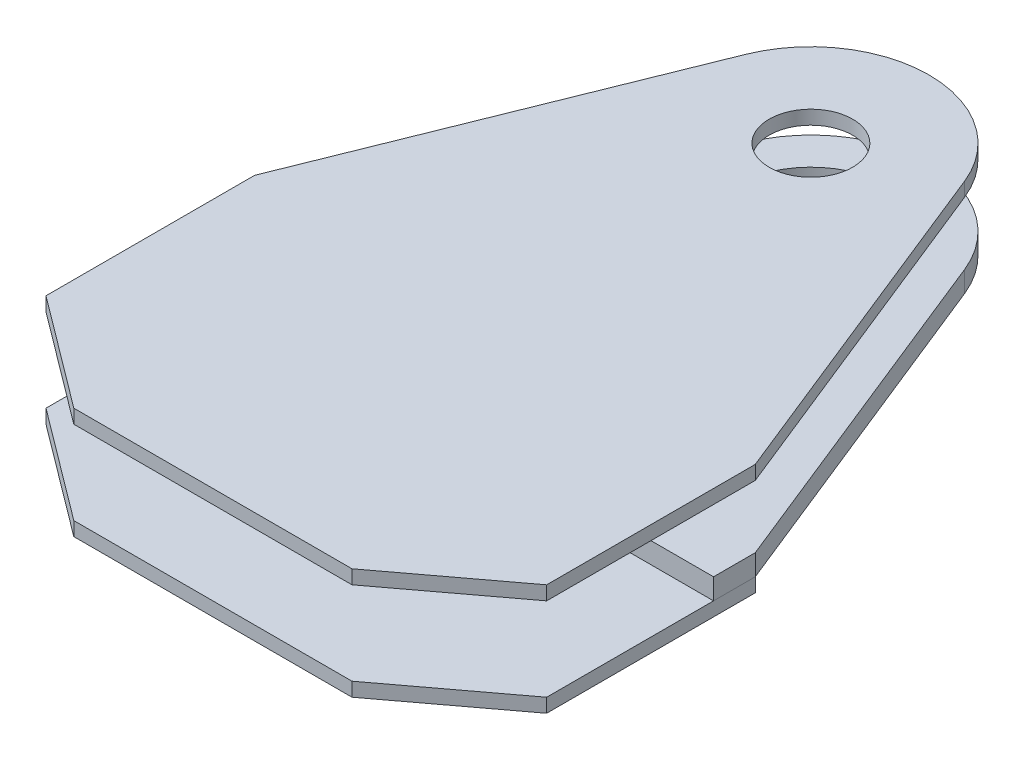
SolidWorks part; units mm, degrees
material "Alum Plate"
ref_plane "Front Plane" through (0, 0, 0) normal (0, 0, 1) x (1, 0, 0)
ref_plane "Top Plane" through (0, 0, 0) normal (0, 1, 0) x (1, 0, 0)
ref_plane "Right Plane" through (0, 0, 0) normal (1, 0, 0) x (0, 0, -1)
other "Center of Mass"
other "Bounding Box"
ref_plane "Default Plane" through (-8.9266, -12.7485, 0) normal (-0.1736, 0.9848, 0) x (0.9848, 0.1736, 0)
sketch "Sketch1" plane through (0, 0, 0) normal (0, 1, 0) x (1, 0, 0)
  line L0 (0, 0) -> (0, -177.8) construction
  line L1 (0, -177.8) -> (38.1, -177.8) construction
  line L2 (38.1, -177.8) -> (76.2, -177.8) construction
  line L3 (76.2, -191.8) -> (38.1, -191.8)
  line L4 (76.2, -191.8) -> (76.2, -163.8)
  line L5 (76.2, -163.8) -> (38.1, -163.8)
  line L6 (38.1, -191.8) -> (38.1, -163.8)
  line L7 (76.2, -191.8) -> (38.1, -163.8) construction
  line L8 (76.2, -163.8) -> (38.1, -191.8) construction
  line L9 (114.3, -195.8) -> (76.2, -195.8)
  line L10 (114.3, -195.8) -> (114.3, -159.8)
  line L11 (114.3, -159.8) -> (76.2, -159.8)
  line L12 (76.2, -195.8) -> (76.2, -159.8)
  line L13 (114.3, -195.8) -> (76.2, -159.8) construction
  line L14 (114.3, -159.8) -> (76.2, -195.8) construction
  line L15 (76.2, -177.8) -> (114.3, -177.8) construction
  line L16 (114.3, -177.8) -> (136.525, -177.8) construction
  line L17 (0, -177.8) -> (0, -196.85) construction
  line L18 (127, -215.9) -> (146.05, -215.9)
  line L19 (127, -215.9) -> (127, -139.7)
  line L20 (127, -139.7) -> (146.05, -139.7)
  line L21 (146.05, -215.9) -> (146.05, -139.7)
  line L22 (127, -215.9) -> (146.05, -139.7) construction
  line L23 (127, -139.7) -> (146.05, -215.9) construction
  circle A0 centre (0, 0) radius 165.1
  circle A1 centre (0, 0) radius 15
  circle A2 centre (0, 0) radius 36
  circle A3 centre (0, -196.85) radius 21
  point P5 (0, 36)
  point P6 (0, 165.1)
  point P7 (57.15, -177.8)
  point P16 (95.25, -177.8)
  point P26 (0, 15)
  point P29 (161.4153, -209.55)
  point P30 (0, -199.2951)
  dimension "D1" = 330.2
  dimension "D2" = 30
  dimension "D3" = 72
  dimension "D11" = 114.3
  dimension "D14" = 42
  dimension "D4" = 76.2
  dimension "D5" = 28
  dimension "D6" = 36
  dimension "D7" = 38.1
  dimension "D8" = 38.1
  dimension "D9" = 19.05
  dimension "D10" = 177.8
  dimension "D12" = 12.7
  dimension "D13" = 196.85
sketch "Sketch2" plane through (0, 0, 0) normal (1, 0, 0) x (0, 0, -1)
  line L0 (-250.4083, -38.1) -> (-147.3027, -38.1) construction
  line L1 (-165.1, -25.4) -> (165.1, -25.4)
  line L2 (-165.1, -25.4) -> (-165.1, -34.925)
  line L3 (-165.1, -34.925) -> (165.1, -34.925)
  line L4 (165.1, -25.4) -> (165.1, -34.925)
  line L5 (-165.1, -25.4) -> (165.1, -34.925) construction
  line L6 (-165.1, -34.925) -> (165.1, -25.4) construction
  line L7 (0, 0) -> (0, 32.1528) construction
  line L8 (-36, -19.05) -> (36, -19.05)
  line L9 (-36, -19.05) -> (-36, -0.05)
  line L10 (-36, -0.05) -> (36, -0.05)
  line L11 (36, -19.05) -> (36, -0.05)
  line L12 (-36, -19.05) -> (36, -0.05) construction
  line L13 (-36, -0.05) -> (36, -19.05) construction
  line L14 (-36, -19.05) -> (-177.8, -19.05) construction
  line L15 (-177.8, -19.05) -> (-177.8, 0) construction
  circle A0 centre (-177.8, 0) radius 38.1
  circle A1 centre (-177.8, 0) radius 18
  point P5 (0, -30.1625)
  point P14 (0, -9.55)
  dimension "D1" = 9.525
  dimension "D2" = 3.175
  dimension "D3" = 19
  dimension "D4" = 19.05
ref_plane "Plane1" through (0, -19.05, 0) normal (0, 1, 0) x (1, 0, 0)
sketch "Sketch3" plane through (0, -19.05, 0) normal (0, 1, 0) x (1, 0, 0)
  line L0 (0, -165.1) -> (0, 165.1) construction
  line L1 (50.0834, 20.1234) -> (114.3, -139.7)
  line L2 (114.3, -139.7) -> (114.3, -158.75)
  line L3 (114.3, -158.75) -> (25.4, -158.75)
  line L5 (-25.4, -158.75) -> (-114.3, -158.75)
  line L7 (-114.3, -158.75) -> (-114.3, -139.7)
  line L8 (-114.3, -139.7) -> (-50.0834, 20.1234)
  line L9 (114.3, -177.8) -> (136.525, -177.8) construction
  line L10 (114.3, -195.8) -> (114.3, -159.8) construction
  line L11 (76.2, -177.8) -> (114.3, -177.8) construction
  line L12 (25.4, -158.75) -> (25.4, -183.7591)
  line L14 (-25.4, -158.75) -> (-25.4, -183.7591)
  line L15 (0, 0) -> (0, -177.8) construction
  circle A1 centre (0, 0) radius 36 construction
  circle A3 centre (0, 0) radius 36
  arc A4 (0, 53.975) -> (50.0834, 20.1234) centre (0, 0) cw
  arc A5 (-50.0834, 20.1234) -> (0, 53.975) centre (0, 0) cw
  arc A6 (25.4, -183.7591) -> (-25.4, -183.7591) centre (0, -196.85) ccw
  point P32 (-21.6748, -176.4629)
  dimension "D1" = 53.975
  dimension "D4" = 28.575
  dimension "D2" = 38.1
  dimension "D3" = 19.05
  dimension "D5" = 25.4
extrude "Boss-Extrude1" add sketch "Sketch3" along normal blind 9.525
ref_plane "Plane2" through (0, 19.05, 0) normal (0, 1, 0) x (1, 0, 0)
sketch "Sketch5" plane through (0, 19.05, 0) normal (0, 1, 0) x (1, 0, 0)
  line L0 (-114.3, -158.75) -> (-114.3, -234.95)
  line L1 (-114.3, -234.95) -> (-63.5, -273.05)
  line L2 (-63.5, -273.05) -> (63.5, -273.05)
  line L3 (63.5, -273.05) -> (114.3, -234.95)
  line L4 (114.3, -234.95) -> (114.3, -158.75)
  line L5 (-50.0834, 20.1234) -> (-114.3, -139.7)
  line L6 (-114.3, -139.7) -> (-114.3, -158.75)
  line L7 (-114.3, -158.75) -> (-25.4, -158.75)
  line L8 (114.3, -158.75) -> (114.3, -139.7)
  line L9 (114.3, -139.7) -> (50.0834, 20.1234)
  line L10 (-50.0834, 20.1234) -> (-114.3, -139.7)
  line L11 (-114.3, -139.7) -> (-114.3, -158.75)
  line L13 (114.3, -158.75) -> (114.3, -139.7)
  line L14 (114.3, -139.7) -> (50.0834, 20.1234)
  line L15 (-114.3, -234.95) -> (114.3, -234.95) construction
  line L16 (0, -200250.4083) -> (0, 199852.6973) construction
  line L18 (-25.4, -158.75) -> (-25.4, -183.7591)
  line L20 (25.4, -183.7591) -> (25.4, -158.75)
  line L22 (25.4, -158.75) -> (114.3, -158.75)
  arc A1 (50.0834, 20.1234) -> (-50.0834, 20.1234) centre (0, 0) ccw
  arc A2 (50.0834, 20.1234) -> (-50.0834, 20.1234) centre (0, 0) ccw
  circle A4 centre (0, 0) radius 19.05
  arc A6 (25.4, -183.7591) -> (-25.4, -183.7591) centre (0, -196.85) ccw
  dimension "D5" = 38.1
  dimension "D2" = 76.2
  dimension "D3" = 38.1
  dimension "D4" = 63.5
  dimension "D1" = 0
extrude "Boss-Extrude2" add sketch "Sketch5" along normal blind 6.35 separate body
sketch "Sketch9" plane through (0, -19.05, 0) normal (0, -1, 0) x (1, 0, 0)
  line L0 (-114.3, 139.7) -> (-114.3, 234.95)
  line L1 (-114.3, 234.95) -> (-63.5, 273.05)
  line L2 (-63.5, 273.05) -> (63.5, 273.05)
  line L3 (63.5, 273.05) -> (114.3, 234.95)
  line L4 (114.3, 234.95) -> (114.3, 139.7)
  line L6 (114.3, 139.7) -> (93.8104, 139.7)
  line L7 (-93.8104, 139.7) -> (-114.3, 139.7)
  arc A0 (-93.8104, 139.7) -> (93.8104, 139.7) centre (0, 0) cw
  circle A1 centre (0, 0) radius 165.1 construction
  dimension "D1" = 3.175
extrude "Boss-Extrude5" add sketch "Sketch9" along normal blind 6.35 separate body
sketch "Sketch10" plane through (0, -19.05, 0) normal (0, -1, 0) x (1, 0, 0)
  line L0 (0, 36) -> (0, -36) construction
  circle A0 centre (0, 0) radius 32.825
  circle A1 centre (0, 0) radius 39.175
  circle A2 centre (0, 0) radius 36 construction
  dimension "D1" = 3.175
  dimension "D2" = 3.175
extrude "Boss-Extrude6" add sketch "Sketch10" along normal blind 3.175 separate body
